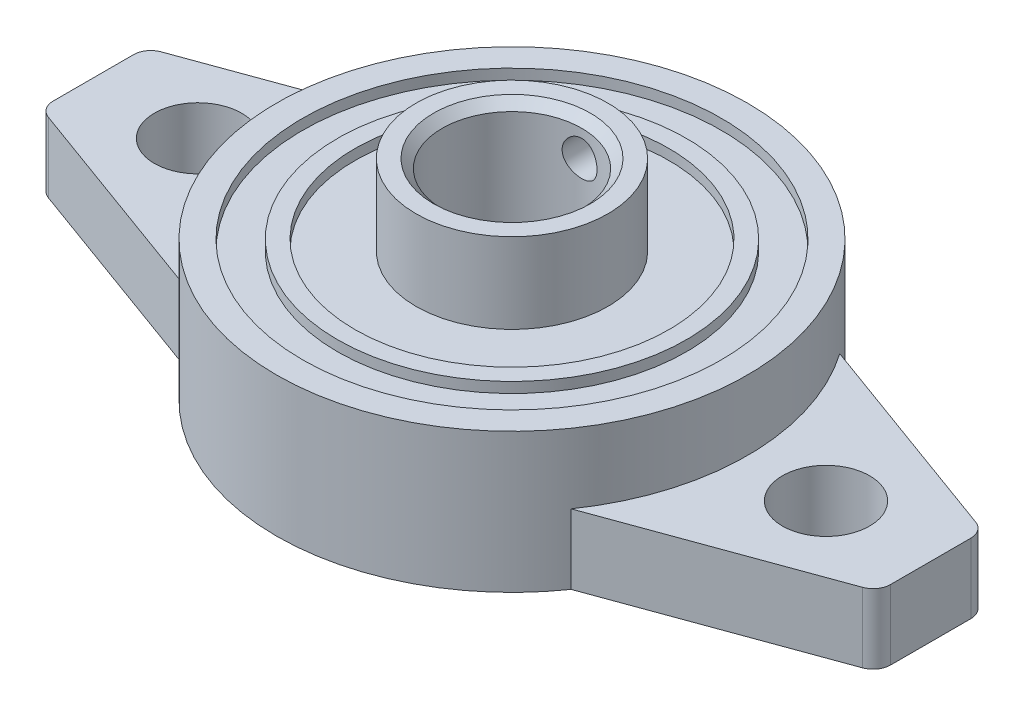
SolidWorks part; units mm, degrees
ref_plane "前视基准面" through (0, 0, 0) normal (0, 0, 1) x (1, 0, 0)
ref_plane "上视基准面" through (0, 0, 0) normal (0, 1, 0) x (1, 0, 0)
ref_plane "右视基准面" through (0, 0, 0) normal (1, 0, 0) x (0, 0, -1)
sketch "草图1" plane through (0, 0, 0) normal (0, 1, 0) x (1, 0, 0)
  line L0 (0, 0) -> (0, 15.5042) construction
  line L1 (-18, 0) -> (18, 0) construction
  line L2 (0, 0) -> (24, 0) construction
  line L3 (24, -2.2998) -> (24, 2.2998)
  line L4 (23.342, 3.2395) -> (11.0894, 7.6991)
  line L5 (23.342, -3.2395) -> (11.0894, -7.6991)
  line L6 (-23.342, 3.2395) -> (-11.0894, 7.6991)
  line L7 (-24, -2.2998) -> (-24, 2.2998)
  line L8 (-23.342, -3.2395) -> (-11.0894, -7.6991)
  circle A0 centre (-18, 0) radius 2.5
  circle A1 centre (18, 0) radius 2.5
  arc A2 (-11.0894, -7.6991) -> (11.0894, -7.6991) centre (0, 0) ccw
  arc A3 (11.0894, 7.6991) -> (-11.0894, 7.6991) centre (0, 0) ccw
  arc A4 (23.342, -3.2395) -> (24, -2.2998) centre (23, -2.2998) ccw
  arc A5 (24, 2.2998) -> (23.342, 3.2395) centre (23, 2.2998) ccw
  arc A6 (-24, -2.2998) -> (-23.342, -3.2395) centre (-23, -2.2998) ccw
  arc A7 (-23.342, 3.2395) -> (-24, 2.2998) centre (-23, 2.2998) ccw
  point P18 (24, -3)
  point P21 (24, 3)
  point P24 (-24, -3)
  point P27 (-24, 3)
  dimension "D2" = 5
  dimension "D3" = 5
  dimension "D4" = 27
  dimension "D8" = 1
  dimension "D1" = 36
  dimension "D5" = 24
  dimension "D6" = 3
  dimension "D7" = 110
extrude "凸台-拉伸1" add sketch "草图1" along normal blind 4
sketch "草图2" plane through (0, 4, 0) normal (0, 1, 0) x (1, 0, 0)
  circle A0 centre (0, 0) radius 13.5
extrude "凸台-拉伸2" add sketch "草图2" along normal blind 4
sketch "草图3" plane through (0, 8, 0) normal (0, 1, 0) x (1, 0, 0)
  circle A0 centre (0, 0) radius 5.5
  point P3 (0, 0)
  dimension "D1" = 11
extrude "凸台-拉伸3" add sketch "草图3" along normal blind 4
sketch "草图4" plane through (0, 12, 0) normal (0, 1, 0) x (1, 0, 0)
  circle A0 centre (0, 0) radius 4
  dimension "D1" = 8
extrude "切除-拉伸1" cut sketch "草图4" against normal through all
sketch "草图5" plane through (0, 8, 0) normal (0, 1, 0) x (1, 0, 0)
  circle A0 centre (0, 0) radius 12
  circle A1 centre (0, 0) radius 10
  circle A2 centre (0, 0) radius 9
  circle M2 centre (0, 0) radius 5.5
  dimension "D1" = 24
  dimension "D2" = 20
  dimension "D3" = 18
extrude "切除-拉伸2" cut sketch "草图5" against normal blind 0.6 contours A0 A1 | A2 M2
sketch "草图8" plane through (0, 0, 0) normal (0, -1, 0) x (1, 0, 0)
  circle A1 centre (0, 0) radius 12.5
  arc A2 (10.2679, 7.1288) -> (-10.2679, 7.1288) centre (0, 0) ccw
  arc A3 (10.2679, 7.1288) -> (-10.2679, 7.1288) centre (0, 0) ccw
  dimension "D1" = 1
extrude "切除-拉伸4" cut sketch "草图8" against normal blind 1 contours A1
sketch "草图9" plane through (0, 0, 0) normal (0, 0, 1) x (1, 0, 0)
  line L0 (0, 12) -> (0, 10) construction
  line L1 (5.5, 12) -> (-5.5, 12) construction
  line L2 (4, 12) -> (-4, 12) construction
  circle A0 centre (0, 10) radius 1
  dimension "D1" = 2
  dimension "D2" = 2
extrude "切除-拉伸5" cut sketch "草图9" against normal through all
chamfer "倒角1" distance 0.5 angle 45 2 edges at (0, 1, -4) (0, 12, 4)
